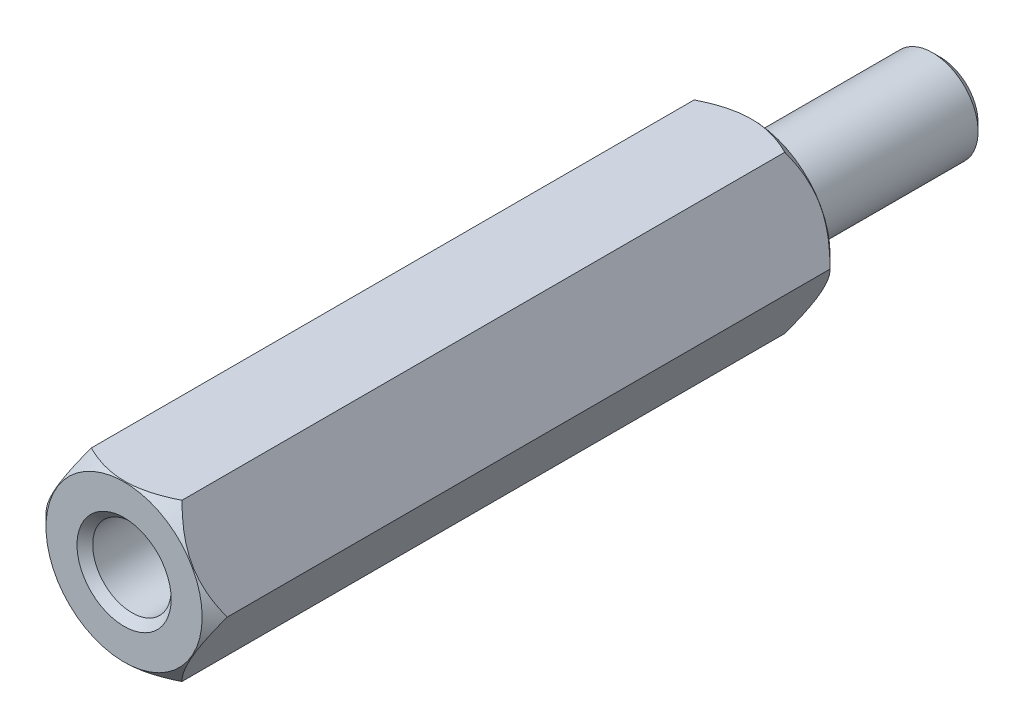
SolidWorks part; units mm, degrees
material "Brass"
ref_plane "Front Plane" through (0, 0, 0) normal (0, 0, 1) x (1, 0, 0)
ref_plane "Top Plane" through (0, 0, 0) normal (0, 1, 0) x (1, 0, 0)
ref_plane "Right Plane" through (0, 0, 0) normal (1, 0, 0) x (0, 0, -1)
ref_axis "Axis1" through (0, 0, 15.2667) along (0, 0, -1)
sketch "Sketch1" plane through (0, 0, 0) normal (0, 0, 1) x (1, 0, 0)
  line L1 (2.8868, 0) -> (1.4434, 2.5)
  line L2 (1.4434, 2.5) -> (-1.4434, 2.5)
  line L3 (-1.4434, 2.5) -> (-2.8868, 0)
  line L4 (-2.8868, 0) -> (-1.4434, -2.5)
  line L5 (-1.4434, -2.5) -> (1.4434, -2.5)
  line L6 (1.4434, -2.5) -> (2.8868, 0)
  circle A0 centre (0, 0) radius 2.5 construction
  dimension "D1" = 5
extrude "HEX" add sketch "Sketch1" along normal mid plane 20
hole_wizard "Tap Drill for M3x0.5 Tap1" positions "Sketch5" profile "Sketch6" hole size "M3x0.5" standard "BSI" end condition through all
sketch "Sketch5" plane through (0, 0, 10) normal (0, 0, 1) x (1, 0, 0)
  point P0 (0, 0)
sketch "Sketch6" plane through (0, 0, 10) normal (1, 0, 0) x (0, -1, 0)
  line L0 (0, 0) -> (0, 20)
  line L1 (0, 20) -> (1.25, 20)
  line L2 (1.25, 20) -> (1.25, 0)
  line L5 (1.25, 0) -> (0, 0)
  line L11 (0, -6.35) -> (0, 107.95) construction
  dimension "Thru Hole Dia." = 2.5
  dimension "Thru Hole Depth" = 20
sketch "Sketch7" plane through (0, 0, 0) normal (0, 1, 0) x (1, 0, 0)
  line L0 (-2.8868, 10) -> (-2.8868, 9.6)
  line L1 (-2.8868, -10) -> (-2.8868, 10) construction
  line L2 (-2.8868, 10) -> (-2.4868, 10)
  line L3 (-1.4434, 10) -> (-2.8868, 10) construction
  line L4 (-2.4868, 10) -> (-2.8868, 9.6)
  dimension "D1" = 0.4
revolve "HexChamfer" cut sketch "Sketch7" angle 360 about axis through (0, 0, 15.2667) along (0, 0, -1)
mirror "Mirror1" about plane through (0, 0, 0) normal (0, 0, 1) of "HexChamfer"
sketch "Sketch8" plane through (0, 0, -10) normal (0, 0, -1) x (-1, 0, 0)
  circle A0 centre (0, 0) radius 1.45
  dimension "D1" = 2.9
extrude "Thread" add sketch "Sketch8" along normal blind 6 and the other way blind 2
chamfer "InnerChamfer" distance 0.25 angle 45 3 edges at (1.25, 0, 10) (-1.45, 0, -16) (1.45, 0, -10)
